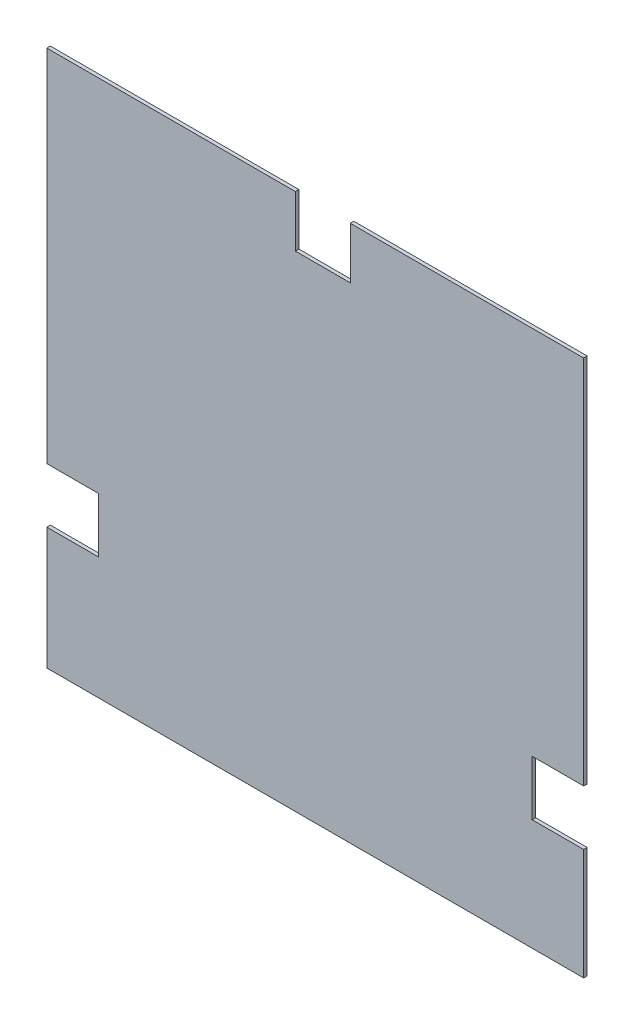
SolidWorks part; units mm, degrees
ref_plane "Front Plane" through (0, 0, 0) normal (0, 0, 1) x (1, 0, 0)
ref_plane "Top Plane" through (0, 0, 0) normal (0, 1, 0) x (1, 0, 0)
ref_plane "Right Plane" through (0, 0, 0) normal (1, 0, 0) x (0, 0, -1)
sketch "Sketch1" plane through (0, 0, 0) normal (0, 0, 1) x (1, 0, 0)
  line L0 (-10, 43) -> (-470, 43) construction
  line L1 (-10, 503) -> (-209.9538, 503)
  line L2 (-10, 503) -> (-10, 185.45)
  line L3 (-10, 43) -> (-470, 43)
  line L4 (-470, 503) -> (-470, 194.65)
  line L5 (-10, 43) -> (-10, 503) construction
  line L6 (-470, 503) -> (-10, 503) construction
  line L7 (-10, 138.35) -> (-54.1805, 138.35)
  line L8 (-54.1805, 138.35) -> (-54.1805, 185.45)
  line L9 (-54.1805, 185.45) -> (-10, 185.45)
  line L10 (-11, 184.45) -> (-10, 185.45) construction
  line L11 (-10, 138.35) -> (-10, 43)
  line L12 (-209.9538, 458.8195) -> (-209.9538, 503)
  line L13 (-209.9538, 458.8195) -> (-257.0538, 458.8195)
  line L14 (-257.0538, 458.8195) -> (-257.0538, 503)
  line L15 (-257.0538, 503) -> (-470, 503)
  line L16 (-425.8195, 147.55) -> (-470, 147.55)
  line L17 (-425.8195, 194.65) -> (-425.8195, 147.55)
  line L18 (-425.8195, 194.65) -> (-470, 194.65)
  line L19 (-470, 147.55) -> (-470, 43)
extrude "Boss-Extrude1" add sketch "Sketch1" against normal blind 3
